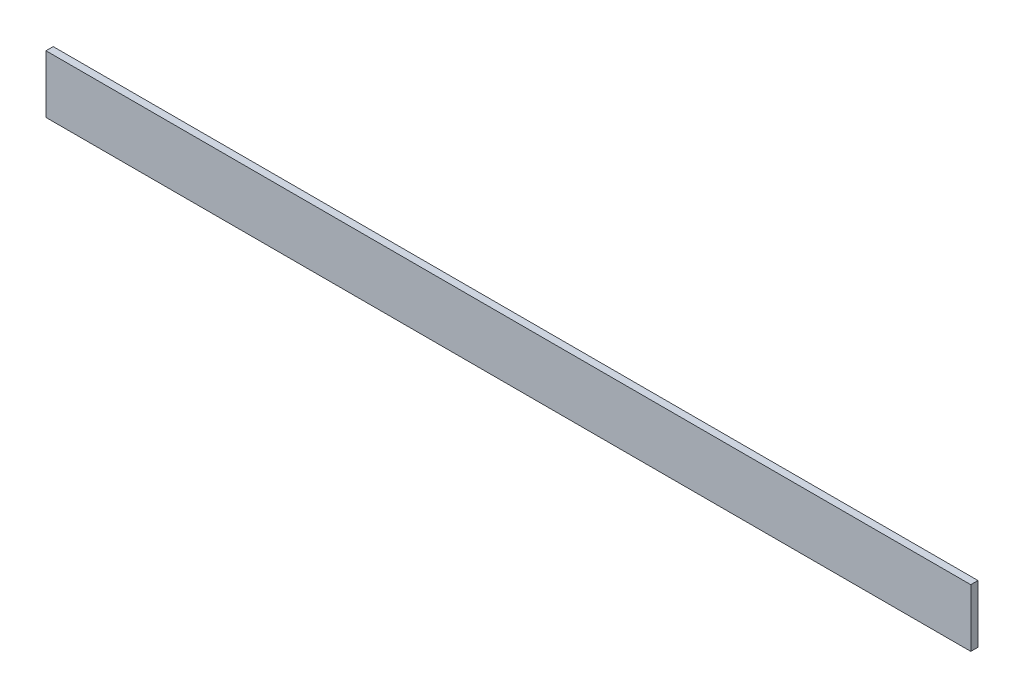
SolidWorks part; units mm, degrees
ref_plane "Plan de face" through (0, 0, 0) normal (0, 0, 1) x (1, 0, 0)
ref_plane "Plan de dessus" through (0, 0, 0) normal (0, 1, 0) x (1, 0, 0)
ref_plane "Plan de droite" through (0, 0, 0) normal (1, 0, 0) x (0, 0, -1)
sketch "Esquisse1" plane through (0, 0, 0) normal (0, 0, 1) x (1, 0, 0)
  line L1 (-320, -20) -> (320, -20)
  line L2 (-320, -20) -> (-320, 20)
  line L3 (-320, 20) -> (320, 20)
  line L4 (320, -20) -> (320, 20)
  line L5 (-320, -20) -> (320, 20) construction
  line L6 (-320, 20) -> (320, -20) construction
  point P0 (0, 0)
  dimension "D1" = 640
  dimension "D2" = 40
extrude "Boss.-Extru.1" add sketch "Esquisse1" along normal blind 5
